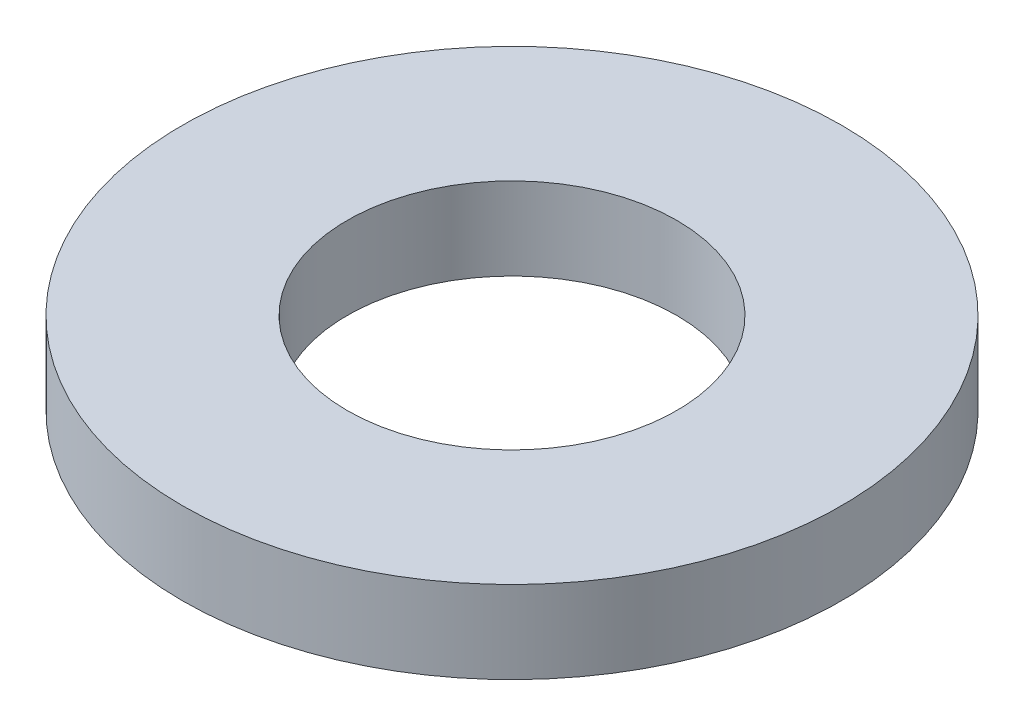
SolidWorks part; units mm, degrees
ref_plane "Front Plane" through (0, 0, 0) normal (0, 0, 1) x (1, 0, 0)
ref_plane "Top Plane" through (0, 0, 0) normal (0, 1, 0) x (1, 0, 0)
ref_plane "Right Plane" through (0, 0, 0) normal (1, 0, 0) x (0, 0, -1)
sketch "Sketch1" plane through (0, 0, 0) normal (0, 1, 0) x (1, 0, 0)
  circle A0 centre (0, 0) radius 3
  circle A1 centre (0, 0) radius 6
  dimension "D1" = 6
  dimension "D2" = 12
extrude "Boss-Extrude1" add sketch "Sketch1" along normal blind 1.5
